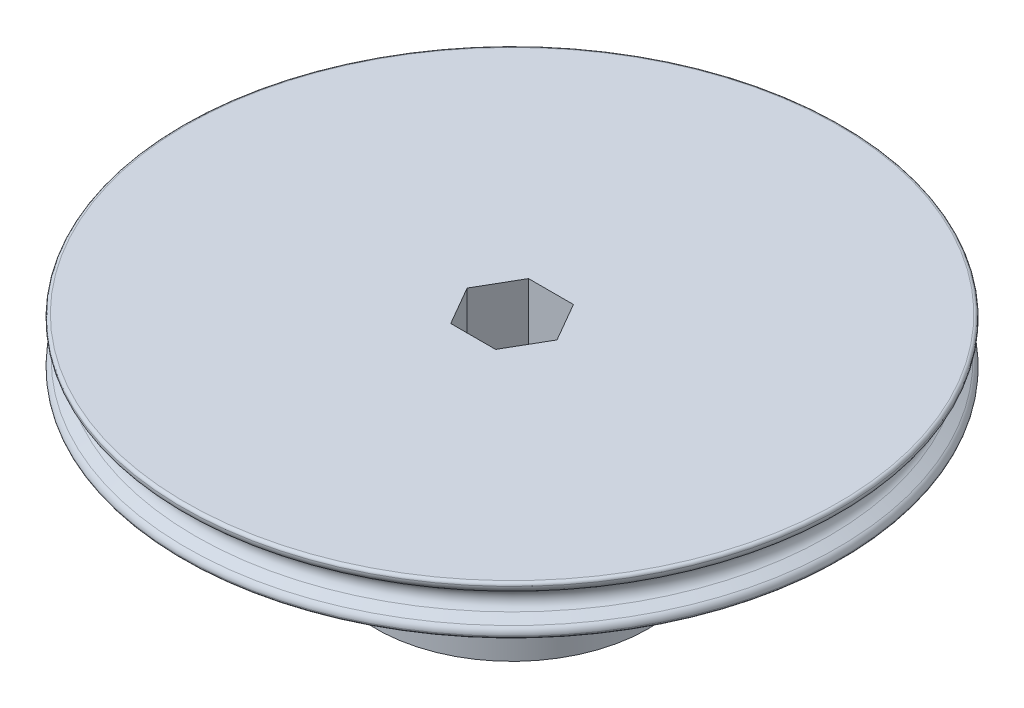
SolidWorks part; units mm, degrees
ref_plane "Front Plane" through (0, 0, 0) normal (0, 0, 1) x (1, 0, 0)
ref_plane "Top Plane" through (0, 0, 0) normal (0, 1, 0) x (1, 0, 0)
ref_plane "Right Plane" through (0, 0, 0) normal (1, 0, 0) x (0, 0, -1)
sketch "Sketch1" plane through (0, 0, 0) normal (0, 0, 1) x (0, 1, 0)
  line L0 (0, 0) -> (0, 17451.5356) construction
  line L1 (4, 0) -> (-4, 0)
  line L2 (-4, 0) -> (-4, 53.3006)
  line L3 (4, 0) -> (4, 53.3006)
  line L6 (-2.4257, 53.2015) -> (-1.5588, 51.7)
  line L7 (2.4257, 53.2015) -> (1.5588, 51.7)
  arc A0 (-4, 53.3006) -> (-3.525, 53.8) centre (-3.5, 53.3006) cw
  arc A1 (4, 53.3006) -> (3.525, 53.8) centre (3.5, 53.3006) ccw
  arc A2 (-3.525, 53.8) -> (-2.4257, 53.2015) centre (-3.465, 52.6015) cw
  arc A3 (3.525, 53.8) -> (2.4257, 53.2015) centre (3.465, 52.6015) ccw
  arc A4 (-1.5588, 51.7) -> (1.5588, 51.7) centre (0, 52.6) ccw
  point P6 (0, 0)
  point P18 (0, 50.8)
  dimension "D2" = 0.5
  dimension "D4" = 1.2
  dimension "D5" = 1.8
  dimension "D1" = 8
  dimension "D3" = 50.8
  dimension "D6" = 3
  dimension "D7" = 60
revolve "Revolve1" add sketch "Sketch1" angle 360 about L1
sketch "Sketch2" plane through (0, -4, 0) normal (0, -1, 0) x (1, 0, 0)
  line L1 (7.3323, 0) -> (3.6662, 6.35)
  line L2 (3.6662, 6.35) -> (-3.6662, 6.35)
  line L3 (-3.6662, 6.35) -> (-7.3323, 0)
  line L4 (-7.3323, 0) -> (-3.6662, -6.35)
  line L5 (-3.6662, -6.35) -> (3.6662, -6.35)
  line L6 (3.6662, -6.35) -> (7.3323, 0)
  circle A1 centre (0, 0) radius 53.3006
  circle A2 centre (0, 0) radius 53.3006
  circle A3 centre (0, 0) radius 6.35 construction
  dimension "D2" = 12.7
  dimension "D1" = 0
extrude "Cut-Extrude2" cut sketch "Sketch2" against normal through all contours L1 L2 L3 L4 L5 L6
sketch "Sketch3" plane through (0, -4, 0) normal (0, -1, 0) x (1, 0, 0)
  line L1 (-3.6662, 6.35) -> (-7.3323, 0)
  line L2 (-7.3323, 0) -> (-3.6662, -6.35)
  line L3 (-3.6662, -6.35) -> (3.6662, -6.35)
  line L4 (3.6662, -6.35) -> (7.3323, 0)
  line L5 (7.3323, 0) -> (3.6662, 6.35)
  line L6 (3.6662, 6.35) -> (-3.6662, 6.35)
  circle A0 centre (0, 0) radius 22.225
  circle A1 centre (0, 0) radius 6.35 construction
  dimension "D1" = 44.45
extrude "Boss-Extrude1" add sketch "Sketch3" along normal blind 25.4
